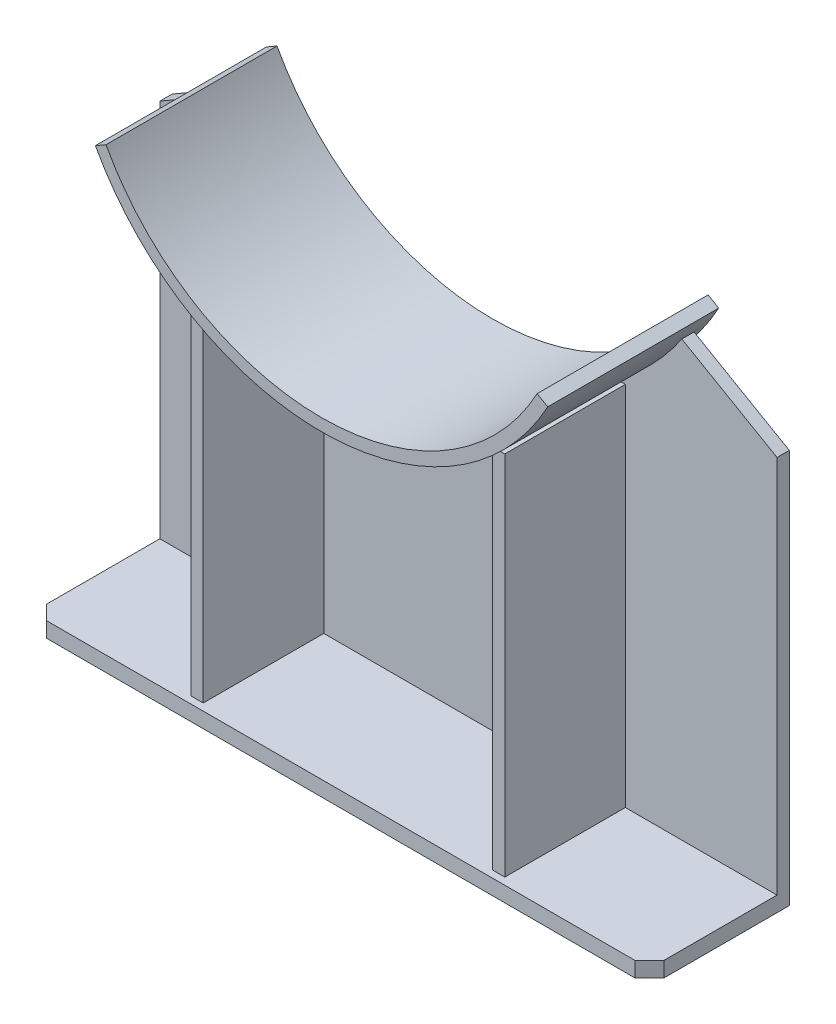
SolidWorks part; units mm, degrees
material "AISI 304"
ref_plane "Front Plane" through (0, 0, 0) normal (0, 0, 1) x (1, 0, 0)
ref_plane "Top Plane" through (0, 0, 0) normal (0, 1, 0) x (1, 0, 0)
ref_plane "Right Plane" through (0, 0, 0) normal (1, 0, 0) x (0, 0, -1)
sketch "Sketch1" plane through (0, 0, 0) normal (0, 0, 1) x (1, 0, 0)
  line L0 (320, 0.3138) -> (-320, 0.3138)
  line L1 (-320, 0.3138) -> (-320, 393.3138)
  line L5 (320, 0.3138) -> (320, 393.3138)
  line L6 (-320, 393.3138) -> (-221.2731, 450.3138)
  line L7 (320, 393.3138) -> (221.2731, 450.3138)
  arc A3 (-221.2731, 450.3138) -> (221.2731, 450.3138) centre (0, 599.2) ccw
  dimension "D5" = 450
  dimension "D4" = 533.4
  dimension "D1" = 599.2
  dimension "D2" = 393
  dimension "D3" = 640
  dimension "D6" = 450
  dimension "D7" = 60
  dimension "D8" = 60
extrude "Boss-Extrude1" add sketch "Sketch1" along normal blind 12.7
sketch "Sketch2" plane through (0, 0, 12.7) normal (0, 0, 1) x (1, 0, 0)
  line L2 (234.5206, 472.2) -> (223.5177, 478.5525)
  line L3 (-223.5177, 478.5525) -> (-234.5206, 472.2)
  line L4 (0, 0) -> (0, 472.2) construction
  arc A0 (-221.2731, 450.3138) -> (221.2731, 450.3138) centre (0, 599.2) ccw construction
  arc A1 (-234.5206, 472.2) -> (234.5206, 472.2) centre (0, 599.2) ccw
  arc A2 (-223.5177, 478.5525) -> (223.5177, 478.5525) centre (0, 599.2) ccw
  arc A3 (-249.9818, 506.2593) -> (234.5206, 472.2) centre (0, 599.2) ccw construction
  arc A4 (-238.0779, 510.685) -> (223.3529, 478.2476) centre (0, 599.2) ccw construction
  dimension "D2" = 60
  dimension "D3" = 60
  dimension "D4" = 472.2
  dimension "D1" = 12.7
extrude "Boss-Extrude2" add sketch "Sketch2" against normal blind 25 and the other way blind 152.3
sketch "Sketch3" plane through (0, 0.3138, 0) normal (0, -1, 0) x (1, 0, 0)
  line L1 (-305, -15) -> (305, -15)
  line L2 (320, 0) -> (320, 130)
  line L3 (305, 145) -> (-305, 145)
  line L4 (-320, 130) -> (-320, 0)
  line L6 (-305, 145) -> (-320, 130)
  line L7 (320, 130) -> (305, 145)
  line L8 (305, -15) -> (320, 0)
  line L9 (-320, 0) -> (-305, -15)
  line L10 (-320, 0) -> (320, 0) construction
  point P1 (-320, -15)
  point P4 (320, -15)
  point P5 (320, 145)
  point P7 (-320, 145)
  point P18 (0, -15)
  dimension "D1" = 15
  dimension "D2" = 15
  dimension "D3" = 45
  dimension "D4" = 45
  dimension "D5" = 15
  dimension "D6" = 45
  dimension "D7" = 15
  dimension "D8" = 45
  dimension "D9" = 160
  dimension "D10" = 15
extrude "Boss-Extrude3" add sketch "Sketch3" along normal blind 15.8
sketch "Sketch4" plane through (0, 0, 12.7) normal (0, 0, 1) x (1, 0, 0)
  line L0 (-320, 0.3138) -> (320, 0.3138) construction
  line L1 (-162.7, 0.3138) -> (-150, 0.3138)
  line L2 (-162.7, 0.3138) -> (-162.7, 380.3138)
  line L3 (-162.7, 380.3138) -> (-150, 380.3138)
  line L4 (-150, 0.3138) -> (-150, 380.3138)
  line L5 (305, 0.3138) -> (-305, 0.3138) construction
  line L6 (150, 0.3138) -> (162.7, 0.3138)
  line L7 (150, 0.3138) -> (150, 380.3138)
  line L8 (150, 380.3138) -> (162.7, 380.3138)
  line L9 (162.7, 0.3138) -> (162.7, 380.3138)
  line L10 (-320, 393.3138) -> (-320, 0.3138) construction
  line L11 (320, 0.3138) -> (320, 393.3138) construction
  dimension "D1" = 12.7
  dimension "D2" = 12.7
  dimension "D3" = 157.3
  dimension "D4" = 157.3
  dimension "D5" = 380
  dimension "D6" = 380
extrude "Boss-Extrude4" add sketch "Sketch4" along normal blind 125
